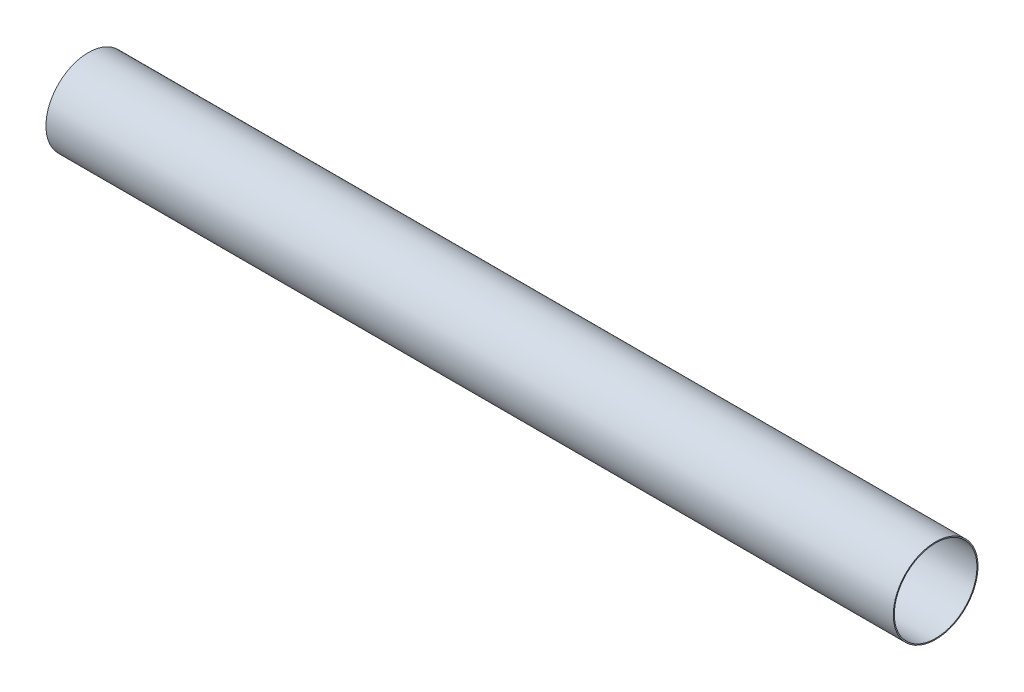
SolidWorks part; units mm, degrees
material "6061-T6 (SS)"
ref_plane "Front Plane" through (0, 0, 0) normal (0, 0, 1) x (1, 0, 0)
ref_plane "Top Plane" through (0, 0, 0) normal (0, 1, 0) x (1, 0, 0)
ref_plane "Right Plane" through (0, 0, 0) normal (1, 0, 0) x (0, 0, -1)
sketch "Sketch1" plane through (0, 0, 0) normal (1, 0, 0) x (0, 0, -1)
  circle A0 centre (0, 0) radius 152.4
  circle A1 centre (0, 0) radius 148.59
  dimension "D2" = 304.8
  dimension "D1" = 297.18
extrude "Boss-Extrude1" add sketch "Sketch1" along normal blind 3048 contours A1
equation "\"P\"= 600'tank pressure in psi"
equation "\"D\"= 12in'rocket diameter, in"
equation "\"S\"= 40000'yield strength of aluminum 6061t6, psi"
equation "\"fos\"= 1.5'minimum factor of safety"
equation "\"t\"= 0.15in'new tank wall thickness, Huzel and Huang calcs"
equation "\"height\"= 120in'tank wall height, in"
equation "\"D2@Sketch1\"=\"D\""
equation "\"D1@Boss-Extrude1\"=\"height\""
